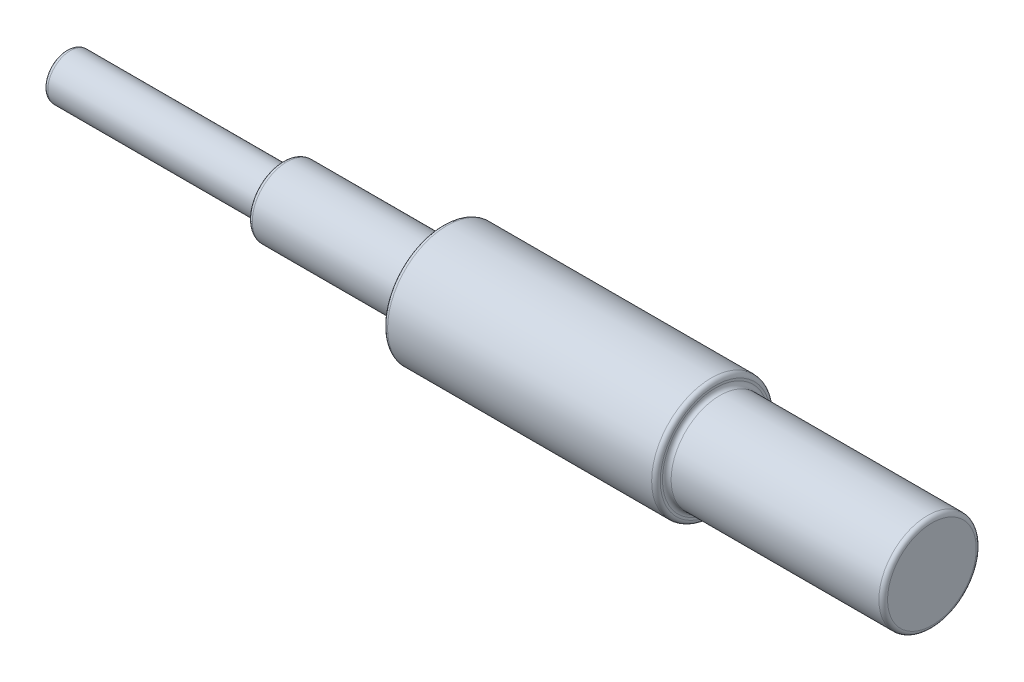
SolidWorks part; units mm, degrees
material "1023 Carbon Steel Sheet (SS)"
ref_plane "Front Plane" through (0, 0, 0) normal (0, 0, 1) x (1, 0, 0)
ref_plane "Top Plane" through (0, 0, 0) normal (0, 1, 0) x (1, 0, 0)
ref_plane "Right Plane" through (0, 0, 0) normal (1, 0, 0) x (0, 0, -1)
sketch "Sketch1" plane through (0, 0, 0) normal (0, 1, 0) x (1, 0, 0)
  line L0 (0, 0) -> (0, 10.5)
  line L1 (0, 10.5) -> (100, 10.5)
  line L2 (100, 10.5) -> (100, 16)
  line L3 (200, 27.5) -> (173.9942, 27.5)
  line L4 (0, 0) -> (400, 0) construction
  line L5 (400, 0) -> (400, 22.5)
  line L6 (400, 22.5) -> (300, 22.5)
  line L7 (300, 27.5) -> (300, 22.5)
  line L8 (300, 27.5) -> (200, 27.5)
  line L9 (173.9942, 27.5) -> (173.9942, 16)
  line L10 (173.9942, 16) -> (100, 16)
  line L11 (0, 0) -> (400, 0)
  dimension "D1" = 100
  dimension "D2" = 10.5
  dimension "D3" = 5.5
  dimension "D5" = 400
  dimension "D6" = 22.5
  dimension "D7" = 100
revolve "Revolve1" add sketch "Sketch1" angle 360 about L4
fillet "Fillet4" radius 2 1 edges at (0, 0, 10.5)
fillet "Fillet5" radius 2 7 edges at (400, 0, 22.5) (300, 0, 22.5) (300, 0, 27.5) (173.9942, 0, 27.5) (173.9942, 0, 16) (100, 0, 16) (100, 0, 10.5)
